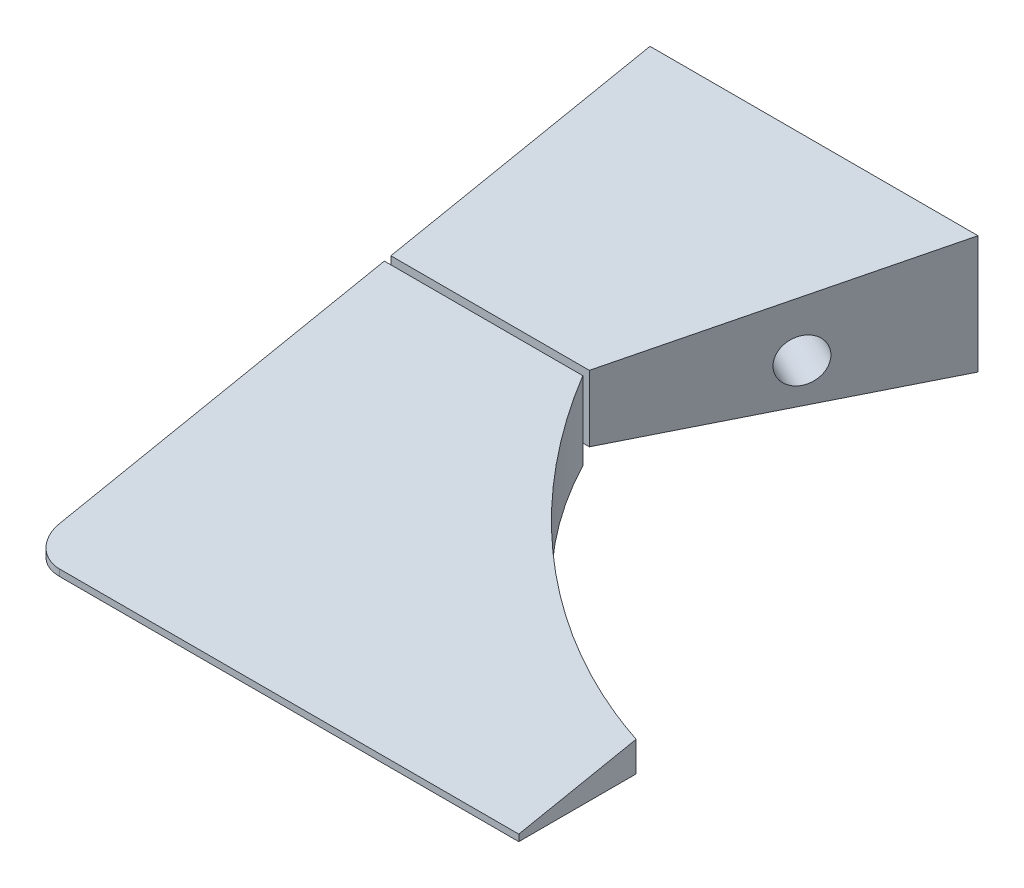
SolidWorks part; units mm, degrees
material "AISI 1020"
ref_plane "Plano frontal" through (0, 0, 0) normal (0, 0, 1) x (1, 0, 0)
ref_plane "Plano superior" through (0, 0, 0) normal (0, 1, 0) x (1, 0, 0)
ref_plane "Plano direito" through (0, 0, 0) normal (1, 0, 0) x (0, 0, -1)
sketch "Esboço1" plane through (0, 0, 0) normal (0, 0, 1) x (1, 0, 0)
  line L1 (-65, 10) -> (65, 10)
  line L2 (-65, 10) -> (-65, -10)
  line L3 (-65, -10) -> (65, -10)
  line L4 (65, 10) -> (65, -10)
  line L5 (-65, 10) -> (65, -10) construction
  line L6 (-65, -10) -> (65, 10) construction
  point P0 (0, 0)
  dimension "D1" = 130
  dimension "D2" = 20
extrude "Ressalto-extrusão1" add sketch "Esboço1" along normal blind 95
sketch "Esboço2" plane through (0, 10, 0) normal (0, 1, 0) x (1, 0, 0)
  line L0 (65, 0) -> (-15, 0)
  line L2 (-65, -95) -> (-65, 0) construction
  line L3 (-35, -40) -> (-15, 0)
  line L4 (65, -95) -> (65, 0) construction
  line L8 (65, -80) -> (65, 0)
  line L11 (30.4043, -80) -> (65, -80)
  arc A1 (30.4043, -80) -> (-35, -40) centre (30.4043, -6.5284) cw
  dimension "D1" = 50
  dimension "D2" = 30
  dimension "D3" = 15
extrude "Corte-extrusão2" cut sketch "Esboço2" against normal up to next contours L3 L0 L8 L11 A1
sketch "Esboço13" plane through (-65, 0, 0) normal (-1, 0, 0) x (0, 0, 1)
  line L0 (0, 10) -> (95, -9)
  line L1 (95, 10) -> (95, -10) construction
  dimension "D1" = 1
extrude "Corte-extrusão4" cut sketch "Esboço13" against normal through all and the other way through all
hole_wizard "Broca de rosquear de cano para tarraxa de 1/84" positions "Esboço14" profile "Esboço15" hole size "1/8" standard "Ansi Inch"
sketch "Esboço14" plane through (-65, 0, 0) normal (-1, 0, 0) x (0, 0, 1)
  line L0 (0, 10) -> (0, -10) construction
  line L1 (95, -10) -> (0, -10) construction
  point P0 (20, -2)
  dimension "D1" = 20
  dimension "D2" = 8
sketch "Esboço15" plane through (-65, -2, 20) normal (0, 1, 0) x (0, 0, 1)
  line L0 (0, 0) -> (0, 11.9768)
  line L1 (0, 11.9768) -> (3.29, 10)
  line L2 (3.29, 10) -> (3.29, 0)
  line L5 (3.29, 0) -> (0, 0)
  line L10 (0, 11.9768) -> (-3.29, 10) construction
  line L11 (0, -6.35) -> (0, 107.95) construction
  dimension "Hole Dia." = 6.58
  dimension "Hole Depth" = 10
  dimension "Drill Angle" = 118
hole_wizard "Broca de rosquear de cano para tarraxa de 1/85" positions "Esboço16" profile "Esboço17" hole size "1/8" standard "Ansi Inch"
sketch "Esboço16" plane through (-12, 0, -6) normal (0.8944, 0, 0.4472) x (0.4472, 0, -0.8944)
  line L0 (-6.7082, -10) -> (-6.7082, 10) construction
  line L1 (-6.7082, -10) -> (-51.4296, -10) construction
  point P0 (-26.7082, -2)
  dimension "D1" = 20
  dimension "D2" = 8
sketch "Esboço17" plane through (-23.9443, -2, 17.8885) normal (0, 1, 0) x (0.4472, 0, -0.8944)
  line L0 (0, 0) -> (0, 11.9768)
  line L1 (0, 11.9768) -> (3.29, 10)
  line L2 (3.29, 10) -> (3.29, 0)
  line L5 (3.29, 0) -> (0, 0)
  line L10 (0, 11.9768) -> (-3.29, 10) construction
  line L11 (0, -6.35) -> (0, 107.95) construction
  dimension "Hole Dia." = 6.58
  dimension "Hole Depth" = 10
  dimension "Drill Angle" = 118
fillet "Filete2" radius 5 1 edges at (-65, -9.5, 95)
sketch "Esboço34" plane through (-65, 0, 0) normal (-1, 0, 0) x (0, 0, 1)
  line L0 (40, 2) -> (40, -10)
  line L4 (39.5, 4.4525) -> (40.5, 4.4525)
  line L5 (39.5, 4.4525) -> (39.5, -12.4525)
  line L6 (39.5, -12.4525) -> (40.5, -12.4525)
  line L7 (40.5, 4.4525) -> (40.5, -12.4525)
  line L8 (39.5, 4.4525) -> (40.5, -12.4525) construction
  line L9 (39.5, -12.4525) -> (40.5, 4.4525) construction
  point P6 (40, -4)
  line M2 (0, -10) -> (90, -10)
  line M4 (90, -8) -> (0, 10)
  dimension "D1" = 1
sketch "Esboço35" plane through (0, 9.6154, 1.9231) normal (0, 0.9806, 0.1961) x (1, 0, 0)
extrude "Corte-extrusão7" cut sketch "Esboço34" against normal through all contours L5 L0 M4 M2 | L7 L0 M4 M2
sketch "Esboço37" plane through (0, 0, 39.5) normal (0, 0, 1) x (1, 0, 0)
  line L0 (-34.7417, 1.9) -> (-65, 1.9) construction
  line L1 (-64, 0.9) -> (-35.7417, 0.9)
  line L2 (-64, 0.9) -> (-64, -7)
  line L3 (-64, -7) -> (-35.7417, -7)
  line L4 (-35.7417, 0.9) -> (-35.7417, -7)
  line L5 (-34.75, -10) -> (-65, -10) construction
  line L7 (-34.7417, -10) -> (-34.7417, 1.9) construction
  line L9 (-65, 1.9) -> (-65, -8) construction
  point P0 (-49.9121, -4.05)
  dimension "D1" = 1
  dimension "D2" = 1
  dimension "D3" = 3
  dimension "D4" = 1
extrude "Ressalto-extrusão2" add sketch "Esboço37" along normal up to next
sketch "Esboço38" plane through (0, 9.6154, 1.9231) normal (0, 0.9806, 0.1961) x (1, 0, 0)
  line L0 (10, -74.0089) -> (10, -95.8565)
  line L2 (10, -95.8565) -> (65, -95.8565)
  line L3 (65, -95.8565) -> (65, -74.0089)
  line L4 (65, -74.0089) -> (10, -74.0089)
  line L6 (-65, -39.3409) -> (-65, -89.8212) construction
  point P9 (0, 0)
  point P11 (0, 0)
  dimension "D1" = 75
extrude "Corte-extrusão8" cut sketch "Esboço38" against normal up to next
sketch "Esboço39" plane through (0, 0, 0) normal (0, 0, -1) x (-1, 0, 0)
  line L0 (15, -10) -> (65, -10)
  line L1 (65, -10) -> (65, -8)
  line L2 (65, -8) -> (15, -8)
  line L3 (15, -10) -> (15, 10) construction
  line L4 (15, -8) -> (15, -10)
extrude "Corte-extrusão9" cut sketch "Esboço39" against normal blind 40.5
